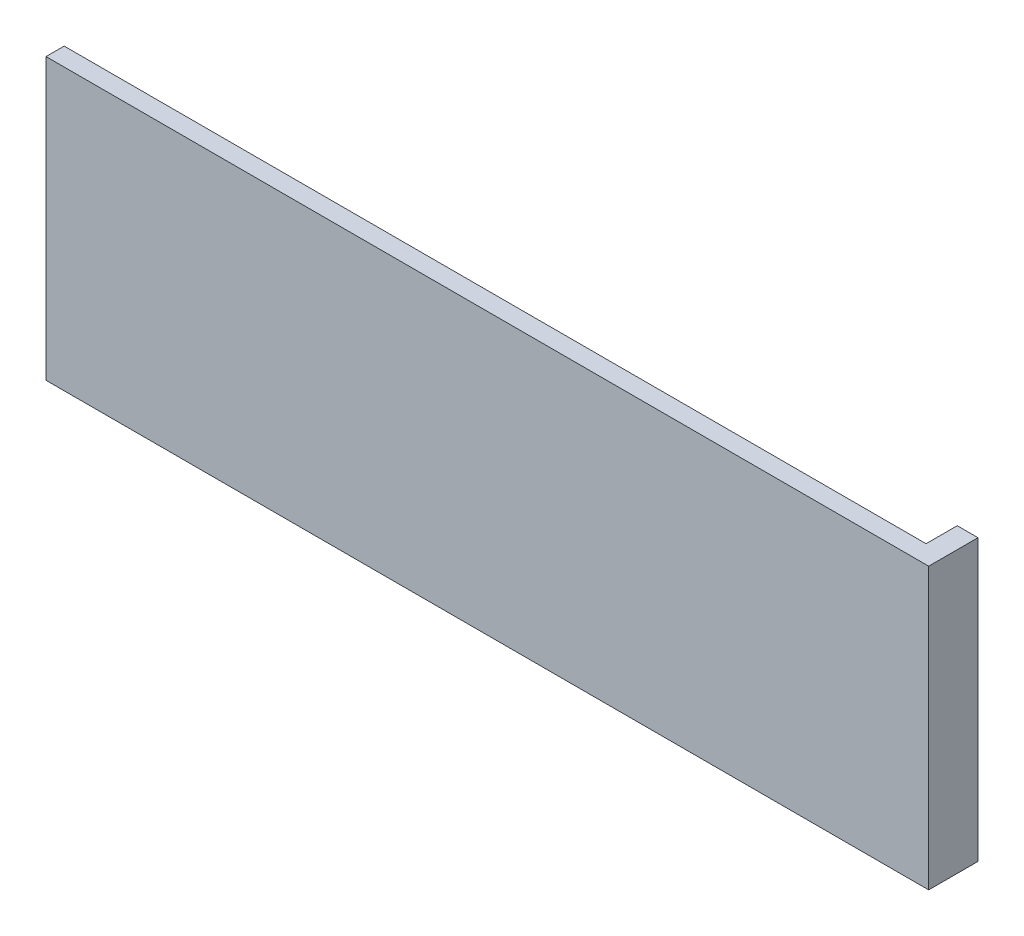
SolidWorks part; units mm, degrees
ref_plane "Plan de face" through (0, 0, 0) normal (0, 0, 1) x (1, 0, 0)
ref_plane "Plan de dessus" through (0, 0, 0) normal (0, 1, 0) x (1, 0, 0)
ref_plane "Plan de droite" through (0, 0, 0) normal (1, 0, 0) x (0, 0, -1)
sketch "Esquisse1" plane through (0, 0, 0) normal (0, 0, 1) x (1, 0, 0)
  line L1 (0, 0) -> (-83, 0)
  line L2 (0, 0) -> (0, 27)
  line L3 (0, 27) -> (-83, 27)
  line L4 (-83, 0) -> (-83, 27)
  dimension "D1" = 83
  dimension "D2" = 27
extrude "Boss.-Extru.1" add sketch "Esquisse1" along normal blind 1.75
other "Déplacer la face1" face at (0, 13.5, 0.875) parameters "D1"=2
sketch "Esquisse3" plane through (0, 0, 0) normal (0, 0, -1) x (-1, 0, 0)
  line L0 (83, 0) -> (-2, 0) construction
  line L1 (-2, 27) -> (0, 27)
  line L2 (-2, 27) -> (-2, 0)
  line L3 (-2, 0) -> (0, 0)
  line L4 (0, 27) -> (0, 0)
  dimension "D1" = 2
extrude "Boss.-Extru.3" add sketch "Esquisse3" along normal blind 3
